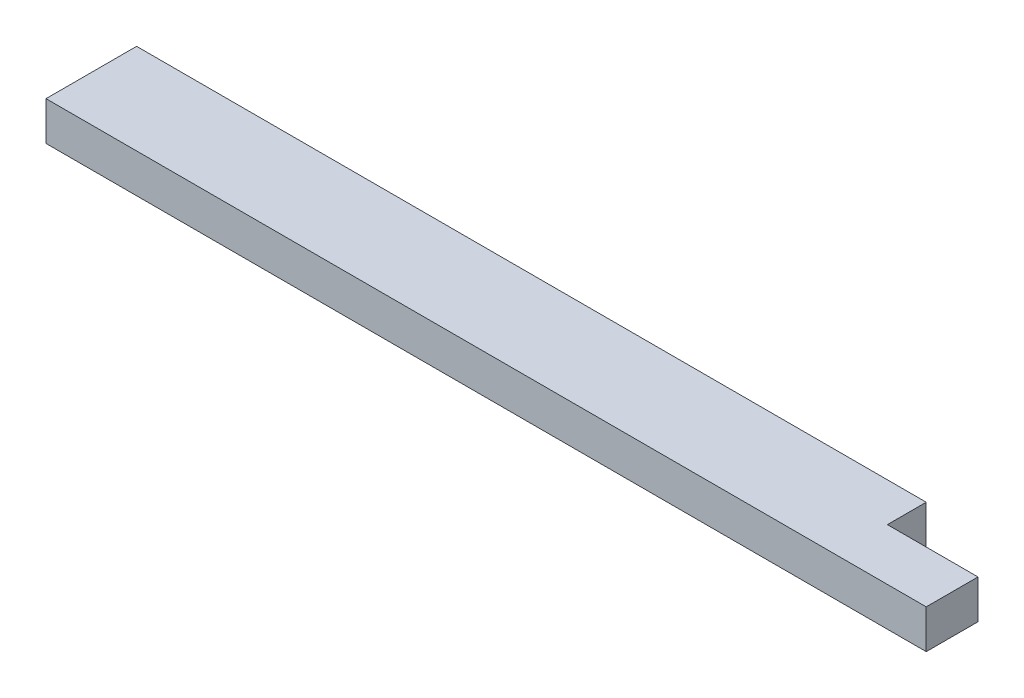
SolidWorks part; units mm, degrees
ref_plane "Front Plane" through (0, 0, 0) normal (0, 0, 1) x (1, 0, 0)
ref_plane "Top Plane" through (0, 0, 0) normal (0, 1, 0) x (1, 0, 0)
ref_plane "Right Plane" through (0, 0, 0) normal (1, 0, 0) x (0, 0, -1)
sketch "Sketch1" plane through (0, 0, 0) normal (0, 1, 0) x (1, 0, 0)
  line L1 (0, 0) -> (863.6, 0)
  line L2 (0, 0) -> (0, 88.9)
  line L3 (0, 88.9) -> (863.6, 88.9)
  line L4 (863.6, 0) -> (863.6, 88.9)
  dimension "D1" = 88.9
  dimension "D2" = 863.6
extrude "Boss-Extrude1" add sketch "Sketch1" along normal blind 38.1
sketch "Sketch3" plane through (0, 38.1, 0) normal (0, 1, 0) x (1, 0, 0)
  line L5 (863.6, 88.9) -> (774.7, 88.9)
  line L6 (863.6, 88.9) -> (863.6, 50.8)
  line L7 (863.6, 50.8) -> (774.7, 50.8)
  line L8 (774.7, 88.9) -> (774.7, 50.8)
  dimension "D2" = 88.9
  dimension "D4" = 38.1
extrude "Cut-Extrude1" cut sketch "Sketch3" against normal through all
